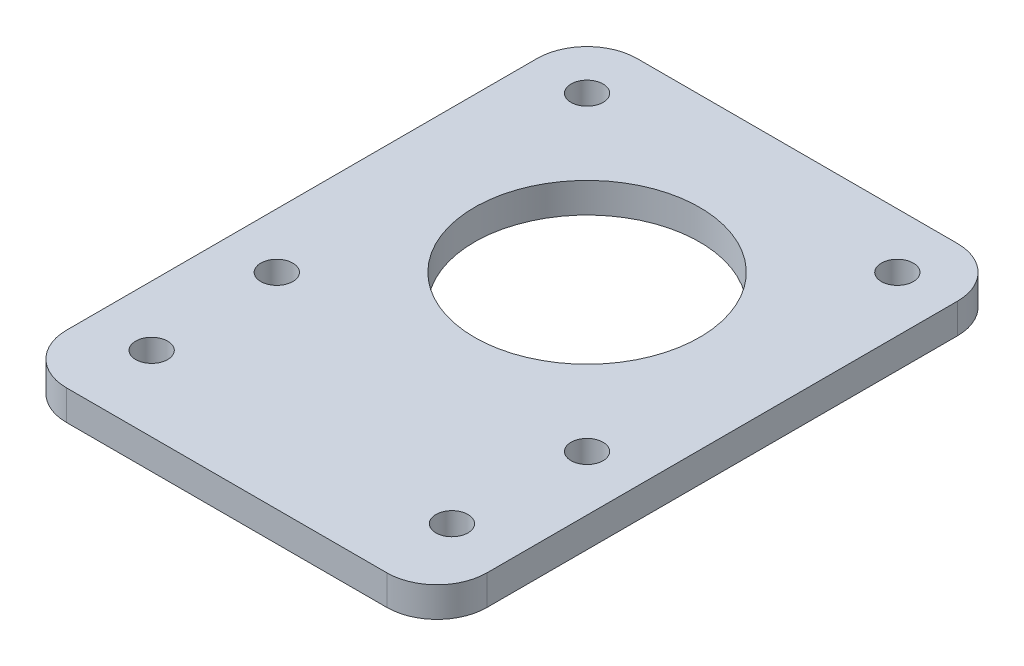
SolidWorks part; units mm, degrees
material "Carbon Fiber"
ref_plane "Front Plane" through (0, 0, 0) normal (0, 0, 1) x (1, 0, 0)
ref_plane "Top Plane" through (0, 0, 0) normal (0, 1, 0) x (1, 0, 0)
ref_plane "Right Plane" through (0, 0, 0) normal (1, 0, 0) x (0, 0, -1)
sketch "Sketch1" plane through (0, 0, 0) normal (0, 1, 0) x (1, 0, 0)
  line L0 (42, 7.5) -> (0, 7.5) construction
  line L1 (0, 0) -> (42, 0)
  line L2 (0, 0) -> (0, 57)
  line L3 (0, 57) -> (42, 57)
  line L4 (42, 0) -> (42, 57)
  line L5 (5.5, 51.5) -> (36.5, 51.5) construction
  line L6 (5.5, 51.5) -> (5.5, 20.5) construction
  line L7 (5.5, 20.5) -> (36.5, 20.5) construction
  line L8 (36.5, 51.5) -> (36.5, 20.5) construction
  line L9 (21, 0) -> (21, 57) construction
  line L10 (0, 15) -> (42, 15) construction
  line L11 (42, 15) -> (36.5, 20.5) construction
  line L12 (36.5, 51.5) -> (42, 57) construction
  line L13 (5.5, 36) -> (36.5, 36) construction
  circle A0 centre (36.5, 51.5) radius 1.6
  circle A1 centre (5.5, 51.5) radius 1.6
  circle A2 centre (5.5, 20.5) radius 1.6
  circle A3 centre (36.5, 20.5) radius 1.6
  circle A4 centre (6, 7.5) radius 1.6
  circle A5 centre (36, 7.5) radius 1.6
  circle A6 centre (21, 36) radius 11.25
  dimension "D3" = 7.5
  dimension "D4" = 30
  dimension "D5" = 3.2
  dimension "D8" = 22.5
  dimension "D1" = 42
  dimension "D2" = 57
  dimension "D6" = 31
  dimension "D7" = 15
extrude "Boss-Extrude1" add sketch "Sketch1" along normal blind 3
fillet "Fillet1" radius 5 4 edges at (0, 1.5, -57) (42, 1.5, -57) (0, 1.5, 0) (42, 1.5, 0)
